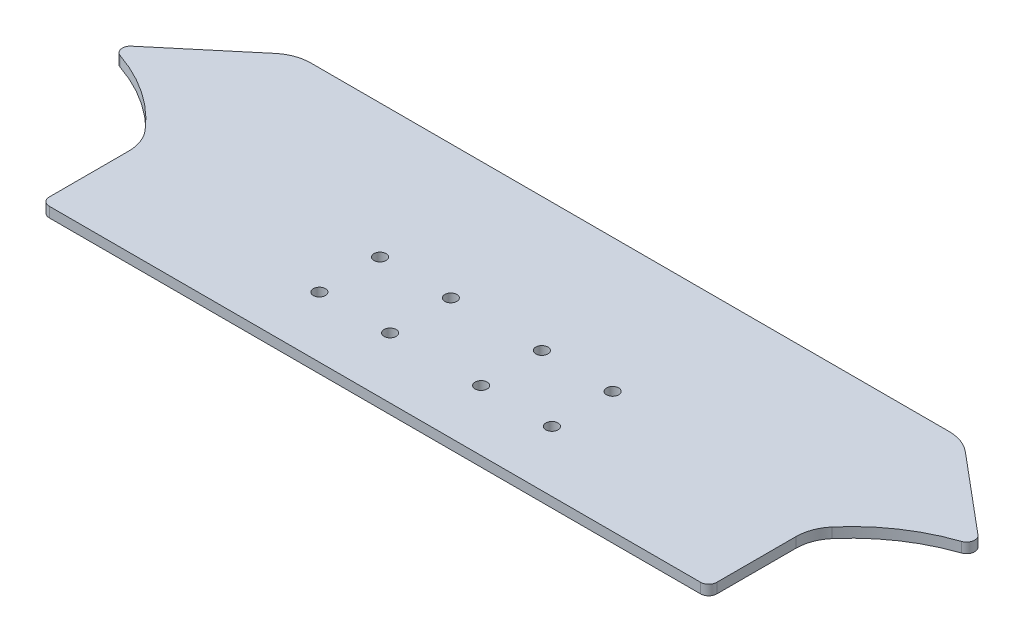
SolidWorks part; units mm, degrees
material "Cast Alloy Steel"
ref_plane "Front Plane" through (0, 0, 0) normal (0, 0, 1) x (1, 0, 0)
ref_plane "Top Plane" through (0, 0, 0) normal (0, 1, 0) x (1, 0, 0)
ref_plane "Right Plane" through (0, 0, 0) normal (1, 0, 0) x (0, 0, -1)
other "Bounding Box"
ref_plane "Default Plane" through (13.8565, 3.175, 6.7999) normal (0, -1, 0) x (-1, 0, 0)
sketch "Sketch1" plane through (0, 0, 0) normal (0, 1, 0) x (1, 0, 0)
  line L1 (-104.775, -40.005) -> (104.775, -40.005)
  line L2 (-104.775, -40.005) -> (-104.775, 40.005)
  line L3 (-104.775, 40.005) -> (104.775, 40.005)
  line L4 (104.775, -40.005) -> (104.775, 40.005)
  line L5 (-104.775, -40.005) -> (104.775, 40.005) construction
  line L6 (-104.775, 40.005) -> (104.775, -40.005) construction
  point P0 (0, 0)
  dimension "D1" = 209.55
  dimension "D2" = 80.01
extrude "Boss-Extrude1" add sketch "Sketch1" along normal blind 3.175
sketch "Sketch2" plane through (0, 3.175, 0) normal (0, 1, 0) x (1, 0, 0)
  line L0 (104.775, 40.005) -> (136.525, 13.3636)
  line L2 (104.775, -8.255) -> (104.775, 40.005)
  line L3 (-104.775, 40.005) -> (-136.525, 13.3636)
  line L5 (-104.775, -8.255) -> (-104.775, 40.005)
  line L6 (104.775, 40.005) -> (-104.775, 40.005) construction
  line L7 (136.525, 13.3636) -> (104.775, 13.3636) construction
  line L8 (-136.525, 13.3636) -> (-104.775, 13.3636) construction
  line L9 (136.525, 13.3636) -> (104.775, -8.255) construction
  line L10 (-104.775, -8.255) -> (-136.525, 13.3636) construction
  line L11 (-104.775, -40.005) -> (104.775, -40.005) construction
  line L12 (104.775, -40.005) -> (104.775, 40.005) construction
  line L13 (-104.775, 40.005) -> (-104.775, -40.005) construction
  line L14 (104.775, -8.255) -> (104.775, -40.005) construction
  line L15 (-104.775, -8.255) -> (-104.775, -40.005) construction
  arc A0 (136.525, 13.3636) -> (104.775, -8.255) centre (149.6286, -40.005) ccw
  arc A1 (-104.775, -8.255) -> (-136.525, 13.3636) centre (-149.6286, -40.005) ccw
  dimension "D1" = 40
  dimension "D2" = 31.75
  dimension "D3" = 31.75
extrude "Boss-Extrude2" add sketch "Sketch2" against normal through all
sketch "Sketch3" plane through (0, 3.175, 0) normal (0, 1, 0) x (1, 0, 0)
  line L0 (36.5125, -1.905) -> (36.5125, -20.955) construction
  line L1 (36.5125, -20.955) -> (14.2875, -20.955) construction
  line L2 (14.2875, -20.955) -> (-14.2875, -20.955) construction
  line L3 (-14.2875, -20.955) -> (-36.5125, -20.955) construction
  line L4 (-36.5125, -20.955) -> (-36.5125, -1.905) construction
  line L5 (-14.2875, -1.905) -> (-14.2875, -20.955) construction
  line L6 (14.2875, -1.905) -> (14.2875, -20.955) construction
  line L7 (0, -20.955) -> (0, -40.005) construction
  line L8 (-104.775, -40.005) -> (104.775, -40.005) construction
  circle A0 centre (36.5125, -20.955) radius 1.8986
  circle A1 centre (14.2875, -20.955) radius 1.8987
  circle A2 centre (-14.2875, -20.955) radius 1.8986
  circle A3 centre (-36.5125, -20.955) radius 1.8986
  circle A4 centre (36.5125, -1.905) radius 1.8986
  circle A5 centre (14.2875, -1.905) radius 1.8987
  circle A6 centre (-14.2875, -1.905) radius 1.8986
  circle A7 centre (-36.5125, -1.905) radius 1.8986
  dimension "D3" = 3.7973
  dimension "D1" = 28.575
  dimension "D2" = 22.225
  dimension "D4" = 19.05
  dimension "D5" = 19.05
extrude "Cut-Extrude1" cut sketch "Sketch3" against normal through all
fillet "Fillet1" radius 12.7 2 edges at (-104.775, 1.5875, 8.255) (104.775, 1.5875, 8.255)
fillet "Fillet2" [suppressed] radius 1.27
sketch "Sketch4" plane through (0, 3.175, 0) normal (0, 1, 0) x (1, 0, 0)
  line L6 (104.775, 40.005) -> (-104.775, 40.005) construction
  line L7 (146.05, 40.005) -> (104.775, 40.005)
  line L8 (146.05, 40.005) -> (146.05, -40.005)
  line L9 (146.05, -40.005) -> (104.775, -40.005)
  line L10 (104.775, 40.005) -> (104.775, -40.005)
  line L11 (146.05, 40.005) -> (104.775, -40.005) construction
  line L12 (146.05, -40.005) -> (104.775, 40.005) construction
  line L13 (-104.775, -40.005) -> (-146.05, -40.005)
  line L14 (-104.775, -40.005) -> (-104.775, 40.005)
  line L15 (-104.775, 40.005) -> (-146.05, 40.005)
  line L16 (-146.05, -40.005) -> (-146.05, 40.005)
  line L17 (-104.775, -40.005) -> (-146.05, 40.005) construction
  line L18 (-104.775, 40.005) -> (-146.05, -40.005) construction
  line L19 (104.775, -40.005) -> (104.775, -12.5911) construction
  line L20 (-104.775, -12.5911) -> (-104.775, -40.005) construction
  point P6 (125.4125, 0)
  point P15 (-125.4125, 0)
  dimension "D2" = 41.275
extrude "Boss-Extrude3" [suppressed] add sketch "Sketch4" against normal through all
fillet "Fillet3" radius 2.54 4 edges at (-136.525, 1.5875, -13.3636) (136.525, 1.5875, -13.3636) (-104.775, 1.5875, 40.005) (104.775, 1.5875, 40.005)
fillet "Fillet4" radius 12.7 2 edges at (-104.775, 1.5875, -40.005) (104.775, 1.5875, -40.005)
